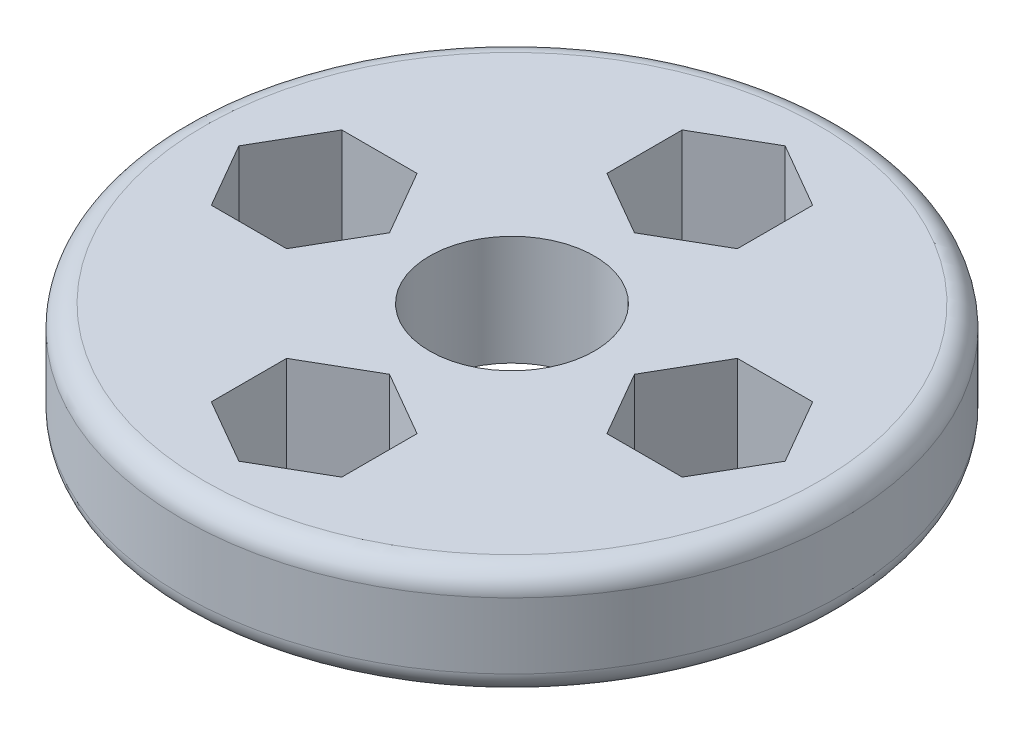
SolidWorks part; units mm, degrees
ref_plane "Front Plane" through (0, 0, 0) normal (0, 0, 1) x (1, 0, 0)
ref_plane "Top Plane" through (0, 0, 0) normal (0, 1, 0) x (1, 0, 0)
ref_plane "Right Plane" through (0, 0, 0) normal (1, 0, 0) x (0, 0, -1)
sketch "Sketch1" plane through (0, 0, 0) normal (0, 1, 0) x (1, 0, 0)
  circle A0 centre (0, 0) radius 30
  dimension "D1" = 60
extrude "Boss-Extrude1" add sketch "Sketch1" along normal blind 10
sketch "Sketch2" plane through (0, 10, 0) normal (0, 1, 0) x (1, 0, 0)
  circle A0 centre (0, 0) radius 7.5
  dimension "D1" = 15
extrude "Cut-Extrude1" cut sketch "Sketch2" against normal through all
fillet "Fillet1" radius 2 2 edges at (0, 0, 30) (0, 10, 30)
sketch "Sketch3" plane through (0, 10, 0) normal (0, 1, 0) x (1, 0, 0)
  line L1 (0, 11.1512) -> (5.9365, 14.5786)
  line L2 (5.9365, 14.5786) -> (5.9365, 21.4335)
  line L3 (5.9365, 21.4335) -> (0, 24.8609)
  line L4 (0, 24.8609) -> (-5.9365, 21.4335)
  line L5 (-5.9365, 21.4335) -> (-5.9365, 14.5786)
  line L6 (-5.9365, 14.5786) -> (0, 11.1512)
  circle A0 centre (0, 18.0061) radius 5.9365 construction
extrude "Cut-Extrude2" cut sketch "Sketch3" against normal through all
pattern_circular "CirPattern1" count 4 over 360 about axis through (0, 0, 0) along (0, 1, 0) of "Cut-Extrude2"
